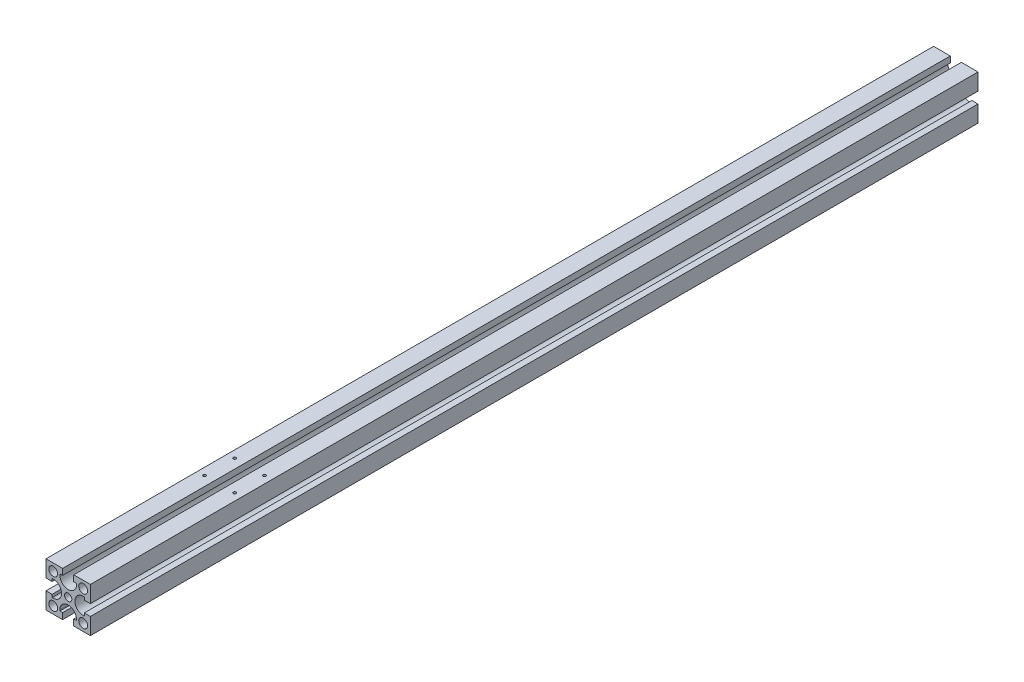
SolidWorks part; units mm, degrees
ref_plane "前基準面" through (0, 0, 0) normal (0, 0, 1) x (1, 0, 0)
ref_plane "上基準面" through (0, 0, 0) normal (0, 1, 0) x (1, 0, 0)
ref_plane "右基準面" through (0, 0, 0) normal (1, 0, 0) x (0, 0, -1)
sketch "草圖1" plane through (0, 0, 0) normal (0, 0, 1) x (1, 0, 0)
  line L0 (0, 20) -> (0, -20) construction
  line L1 (-20, -20) -> (20, -20)
  line L2 (-20, -20) -> (-20, 20)
  line L3 (-20, 20) -> (20, 20)
  line L4 (20, -20) -> (20, 20)
  dimension "D1" = 40
  dimension "D2" = 40
extrude "伸長1" add sketch "草圖1" along normal blind 800
sketch "草圖2" plane through (0, 0, 0) normal (0, 0, -1) x (-1, 0, 0)
  line L0 (-20, 20) -> (20, 20) construction
  line L4 (5, 14.5) -> (7.5, 14.5)
  line L5 (14.5, -5) -> (14.5, -7.5)
  line L6 (-5, 14.5) -> (-5, 20)
  line L7 (-5, 20) -> (5, 20)
  line L8 (5, 14.5) -> (5, 20)
  line L9 (14.5, 5) -> (20, 5)
  line L10 (-7.5, 13.5) -> (-7.5, 14.5)
  line L11 (-7.5, 14.5) -> (-5, 14.5)
  line L12 (7.5, 13.5) -> (7.5, 14.5)
  line L13 (20, 5) -> (20, -5)
  line L14 (14.5, -5) -> (20, -5)
  line L15 (13.5, 7.5) -> (14.5, 7.5)
  line L16 (14.5, 7.5) -> (14.5, 5)
  line L17 (13.5, -7.5) -> (14.5, -7.5)
  line L18 (-5, -14.5) -> (-7.5, -14.5)
  line L19 (5, -14.5) -> (5, -20)
  line L20 (5, -20) -> (-5, -20)
  line L21 (-5, -14.5) -> (-5, -20)
  line L22 (7.5, -13.5) -> (7.5, -14.5)
  line L23 (7.5, -14.5) -> (5, -14.5)
  line L24 (-7.5, -13.5) -> (-7.5, -14.5)
  line L25 (-14.5, 5) -> (-14.5, 7.5)
  line L26 (-14.5, -5) -> (-20, -5)
  line L27 (-20, -5) -> (-20, 5)
  line L28 (-14.5, 5) -> (-20, 5)
  line L29 (-13.5, -7.5) -> (-14.5, -7.5)
  line L30 (-14.5, -7.5) -> (-14.5, -5)
  line L31 (-13.5, 7.5) -> (-14.5, 7.5)
  line L32 (0, -20) -> (0, 0) construction
  line L33 (20, -20) -> (-20, -20) construction
  line L34 (0, 0) -> (-20, 0) construction
  line L35 (-20, -20) -> (-20, 20) construction
  line L36 (20, 20) -> (20, -20) construction
  circle A0 centre (0, 0) radius 3.25
  circle A1 centre (-13.5, 13.5) radius 4
  circle A2 centre (13.5, 13.5) radius 4
  circle A3 centre (-13.5, -13.5) radius 4
  circle A4 centre (13.5, -13.5) radius 4
  arc A5 (-7.5, 13.5) -> (7.5, 13.5) centre (0, 13.5) ccw
  arc A6 (13.5, 7.5) -> (13.5, -7.5) centre (13.5, 0) ccw
  arc A7 (7.5, -13.5) -> (-7.5, -13.5) centre (0, -13.5) ccw
  arc A8 (-13.5, -7.5) -> (-13.5, 7.5) centre (-13.5, 0) ccw
  dimension "D1" = 6.5
  dimension "D2" = 8
  dimension "D5" = 15
  dimension "D12" = 5.5
  dimension "D3" = 27
  dimension "D4" = 27
  dimension "D6" = 10
extrude "除料-伸長1" cut sketch "草圖2" against normal through all
hole_wizard "M3x0.5 螺紋孔1" positions "草圖5" profile "草圖4" tap size "M3x0.5" standard "JIS"
sketch "草圖5" plane through (0, 20, 0) normal (0, 1, 0) x (1, 0, 0)
  line L2 (0, 0) -> (0, -800) construction
  line L5 (13.5, -800) -> (13.5, 0) construction
  line L6 (20, -800) -> (5, -800) construction
  line L7 (20, 0) -> (5, 0) construction
  line L10 (20, -800) -> (20, 0) construction
  line L11 (-13.5, -800) -> (-13.5, 0) construction
  point P25 (13.5, -663.5)
  point P27 (13.5, -636.5)
  point P32 (-13.5, -636.5)
  point P33 (-13.5, -663.5)
  dimension "D1" = 6.5
  dimension "D2" = 27
  dimension "D3" = 136.5
sketch "草圖4" plane through (13.5, 20, 663.5) normal (1, 0, 0) x (0, 0, 1)
  line L0 (0, 0) -> (0, 8.2511)
  line L1 (0, 8.2511) -> (1.25, 7.5)
  line L2 (1.25, 7.5) -> (1.25, 0)
  line L5 (1.25, 0) -> (0, 0)
  line L10 (0, 8.2511) -> (-1.25, 7.5) construction
  line L11 (0, -6.35) -> (0, 107.95) construction
  dimension "螺孔鑽直徑" = 2.5
  dimension "螺孔鑽深度" = 7.5
  dimension "導頭角度" = 118
hole_wizard "M3x0.5 螺紋孔2" positions "草圖7" profile "草圖6" tap size "M3x0.5" standard "JIS"
sketch "草圖7" plane through (0, -20, 0) normal (0, -1, 0) x (-1, 0, 0)
  line L0 (0, 0) -> (0, -800) construction
  line L3 (13.5, -800) -> (13.5, 0) construction
  line L4 (20, -800) -> (5, -800) construction
  line L5 (20, 0) -> (5, 0) construction
  line L8 (20, -800) -> (20, 0) construction
  line L9 (-13.5, -800) -> (-13.5, 0) construction
  point P21 (13.5, -636.5)
  point P23 (13.5, -663.5)
  point P30 (-13.5, -663.5)
  point P31 (-13.5, -636.5)
  dimension "D1" = 800
  dimension "D2" = 27
  dimension "D3" = 6.5
  dimension "D4" = 136.5
sketch "草圖6" plane through (-13.5, -20, 636.5) normal (1, 0, 0) x (0, 0, -1)
  line L0 (0, 0) -> (0, 8.2511)
  line L1 (0, 8.2511) -> (1.25, 7.5)
  line L2 (1.25, 7.5) -> (1.25, 0)
  line L5 (1.25, 0) -> (0, 0)
  line L10 (0, 8.2511) -> (-1.25, 7.5) construction
  line L11 (0, -6.35) -> (0, 107.95) construction
  dimension "螺孔鑽直徑" = 2.5
  dimension "螺孔鑽深度" = 7.5
  dimension "導頭角度" = 118
